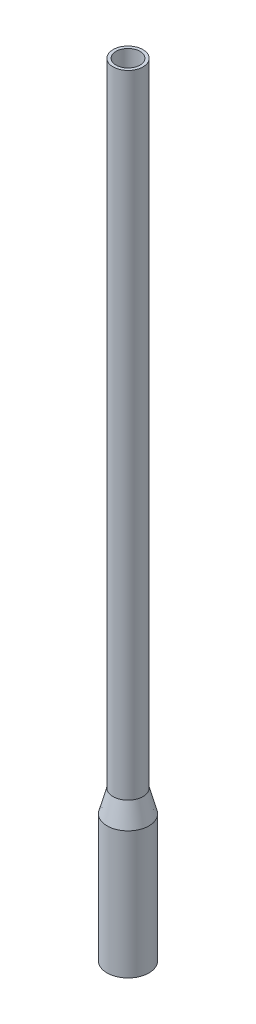
SolidWorks part; units mm, degrees
material "Plain Carbon Steel"
ref_plane "Front Plane" through (0, 0, 0) normal (0, 0, 1) x (1, 0, 0)
ref_plane "Top Plane" through (0, 0, 0) normal (0, 1, 0) x (1, 0, 0)
ref_plane "Right Plane" through (0, 0, 0) normal (1, 0, 0) x (0, 0, -1)
sketch "Sketch1" plane through (0, 0, 0) normal (0, 0, 1) x (1, 0, 0)
  line L0 (0, 0) -> (0, 2110) construction
  line L1 (-70, -74.641) -> (-70, -500)
  line L2 (-50, 0) -> (-50, 2110)
  line L3 (-60, -75.9575) -> (-60, -500)
  line L4 (-40, -1.3165) -> (-60, -75.9575)
  line L5 (-40, -1.3165) -> (-40, 2110)
  line L6 (-50, 0) -> (-70, -74.641)
  line L7 (-70, -500) -> (-60, -500)
  line L8 (-50, 2110) -> (-40, 2110)
  dimension "D1" = 50
  dimension "D2" = 2110
  dimension "D3" = 10
  dimension "D4" = 165
revolve "Revolve1" add sketch "Sketch1" angle 360 about L0
